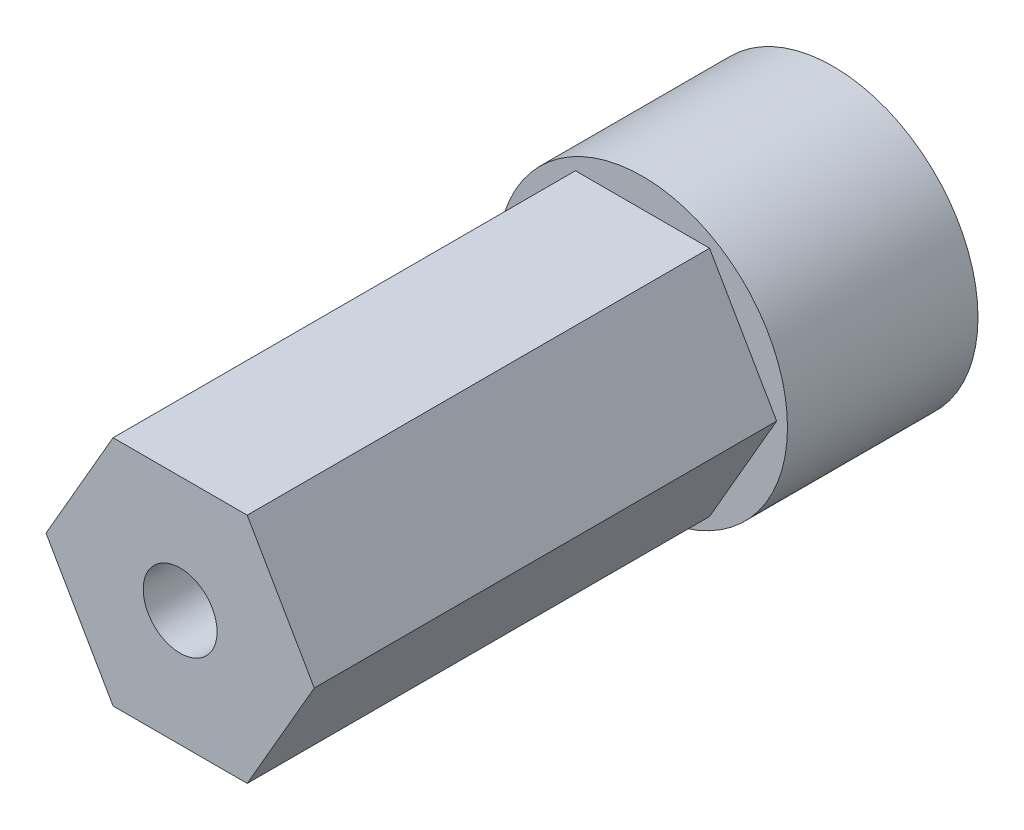
SolidWorks part; units mm, degrees
ref_plane "Front Plane" through (0, 0, 0) normal (0, 0, 1) x (1, 0, 0)
ref_plane "Top Plane" through (0, 0, 0) normal (0, 1, 0) x (1, 0, 0)
ref_plane "Right Plane" through (0, 0, 0) normal (1, 0, 0) x (0, 0, -1)
sketch "Sketch2" plane through (0, 0, 0) normal (0, 0, 1) x (1, 0, 0)
  circle A0 centre (0, 0) radius 7.9248
extrude "Boss-Extrude1" add sketch "Sketch2" along normal blind 10.414
sketch "Sketch3" plane through (0, 0, 10.414) normal (0, 0, 1) x (1, 0, 0)
  line L0 (0, 6.35) -> (0, 0)
  line L1 (7.3323, 0) -> (3.6662, 6.35)
  line L2 (3.6662, 6.35) -> (-3.6662, 6.35)
  line L3 (-3.6662, 6.35) -> (-7.3323, 0)
  line L4 (-7.3323, 0) -> (-3.6662, -6.35)
  line L5 (-3.6662, -6.35) -> (3.6662, -6.35)
  line L6 (3.6662, -6.35) -> (7.3323, 0)
  circle A0 centre (0, 0) radius 6.35 construction
extrude "Boss-Extrude2" add sketch "Sketch3" along normal blind 25.273
sketch "Sketch4" plane through (0, 0, 35.687) normal (0, 0, 1) x (1, 0, 0)
  circle A0 centre (0, 0) radius 2.0193
extrude "Cut-Extrude1" cut sketch "Sketch4" against normal blind 22.86
